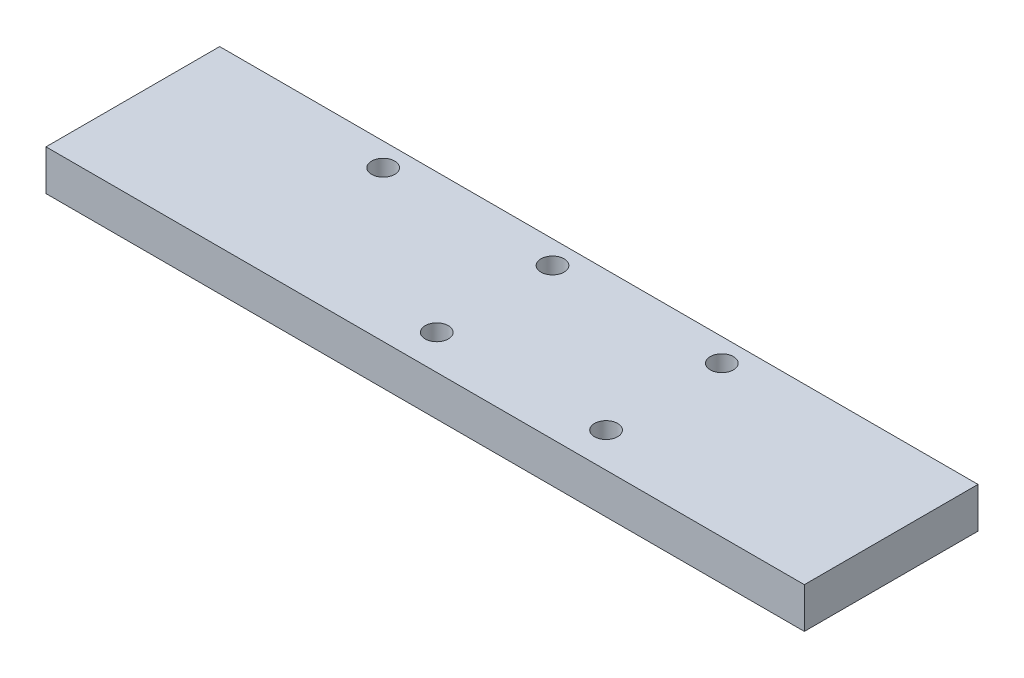
SolidWorks part; units mm, degrees
ref_plane "Front Plane" through (0, 0, 0) normal (0, 0, 1) x (1, 0, 0)
ref_plane "Top Plane" through (0, 0, 0) normal (0, 1, 0) x (1, 0, 0)
ref_plane "Right Plane" through (0, 0, 0) normal (1, 0, 0) x (0, 0, -1)
sketch "Sketch1" plane through (0, 0, 0) normal (0, 1, 0) x (1, 0, 0)
  line L1 (-102.5105, 65.1674) -> (28.4895, 65.1674)
  line L2 (-102.5105, 65.1674) -> (-102.5105, 35.1674)
  line L3 (-102.5105, 35.1674) -> (28.4895, 35.1674)
  line L4 (28.4895, 65.1674) -> (28.4895, 35.1674)
  dimension "D1" = 30
  dimension "D2" = 131
extrude "Boss-Extrude1" add sketch "Sketch1" along normal blind 7 contours L2 L3 L4 L1
sketch "Sketch2" plane through (0, 0, 0) normal (0, -1, 0) x (1, 0, 0)
  line L0 (-102.5105, -65.1674) -> (-102.5105, -35.1674) construction
  line L1 (-102.5105, -65.1674) -> (28.4895, -65.1674) construction
  circle A0 centre (-70.2605, -61.1674) radius 2
  circle A1 centre (-41.0105, -61.1674) radius 2
  circle A2 centre (-11.7605, -61.1674) radius 2
  circle A3 centre (-11.7605, -41.1674) radius 2
  circle A4 centre (-41.0105, -41.1674) radius 2
  dimension "D1" = 32.25
  dimension "D5" = 29.25
  dimension "D2" = 4
  dimension "D3" = 29.25
  dimension "D4" = 4
  dimension "D6" = 4
extrude "Cut-Extrude1" cut sketch "Sketch2" against normal blind 10
